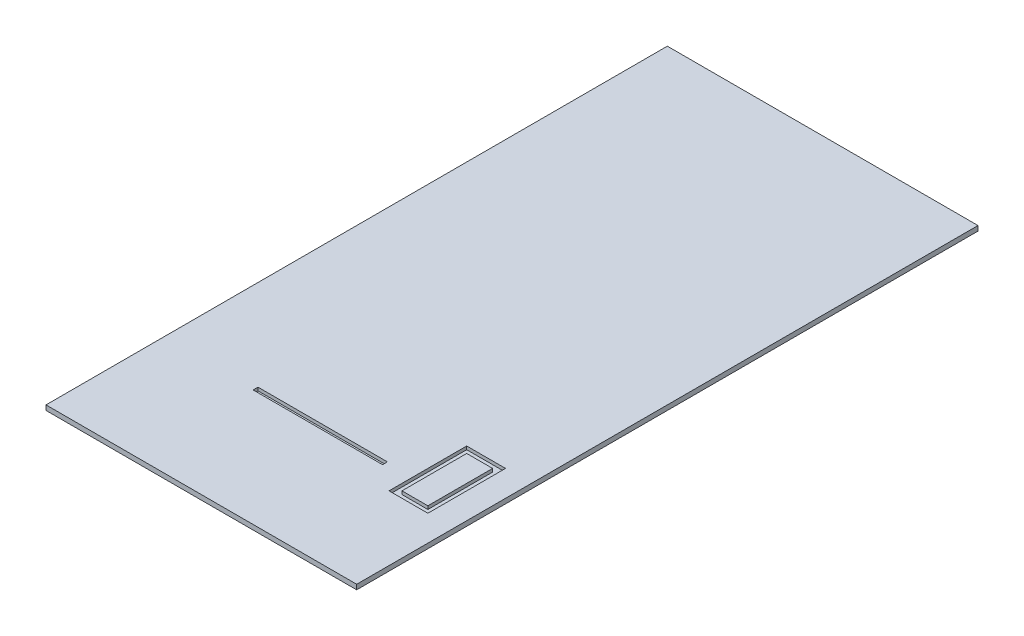
SolidWorks part; units mm, degrees
material "Oak"
ref_plane "Front Plane" through (0, 0, 0) normal (0, 0, 1) x (1, 0, 0)
ref_plane "Top Plane" through (0, 0, 0) normal (0, 1, 0) x (1, 0, 0)
ref_plane "Right Plane" through (0, 0, 0) normal (1, 0, 0) x (0, 0, -1)
sketch "Sketch1" plane through (0, 0, 0) normal (0, 1, 0) x (1, 0, 0)
  line L1 (-609.6, -1219.2) -> (609.6, -1219.2)
  line L2 (-609.6, -1219.2) -> (-609.6, 1219.2)
  line L3 (-609.6, 1219.2) -> (609.6, 1219.2)
  line L4 (609.6, -1219.2) -> (609.6, 1219.2)
  line L5 (-609.6, -1219.2) -> (609.6, 1219.2) construction
  line L6 (-609.6, 1219.2) -> (609.6, -1219.2) construction
  point P0 (0, 0)
  dimension "D1" = 2438.4
  dimension "D2" = 1219.2
extrude "Boss-Extrude1" add sketch "Sketch1" along normal blind 19.05
sketch "Sketch2" plane through (0, 19.05, 0) normal (0, 1, 0) x (1, 0, 0)
  line L0 (-609.6, -1219.2) -> (609.6, -1219.2) construction
  line L1 (508, -838.2) -> (355.6, -838.2)
  line L2 (508, -838.2) -> (508, -533.4)
  line L3 (508, -533.4) -> (355.6, -533.4)
  line L4 (355.6, -838.2) -> (355.6, -533.4)
  line L5 (609.6, -1219.2) -> (609.6, 1219.2) construction
  line L6 (482.6, -558.8) -> (381, -558.8)
  line L7 (381, -812.8) -> (381, -558.8)
  line L8 (482.6, -812.8) -> (381, -812.8)
  line L9 (482.6, -812.8) -> (482.6, -558.8)
  dimension "D1" = 381
  dimension "D2" = 101.6
  dimension "D3" = 152.4
  dimension "D4" = 304.8
  dimension "D5" = 25.4
extrude "Cut-Extrude1" cut sketch "Sketch2" against normal blind 12.7
sketch "Sketch3" plane through (0, 19.05, 0) normal (0, 1, 0) x (1, 0, 0)
  line L0 (0, 0) -> (0, -742.95) construction
  line L1 (-254, -742.95) -> (254, -742.95)
  line L2 (-254, -742.95) -> (-254, -762)
  line L3 (-254, -762) -> (254, -762)
  line L4 (254, -742.95) -> (254, -762)
  line L5 (-609.6, -1219.2) -> (609.6, -1219.2) construction
  dimension "D1" = 19.05
  dimension "D2" = 508
  dimension "D3" = 457.2
extrude "Cut-Extrude2" cut sketch "Sketch3" against normal blind 12.7
